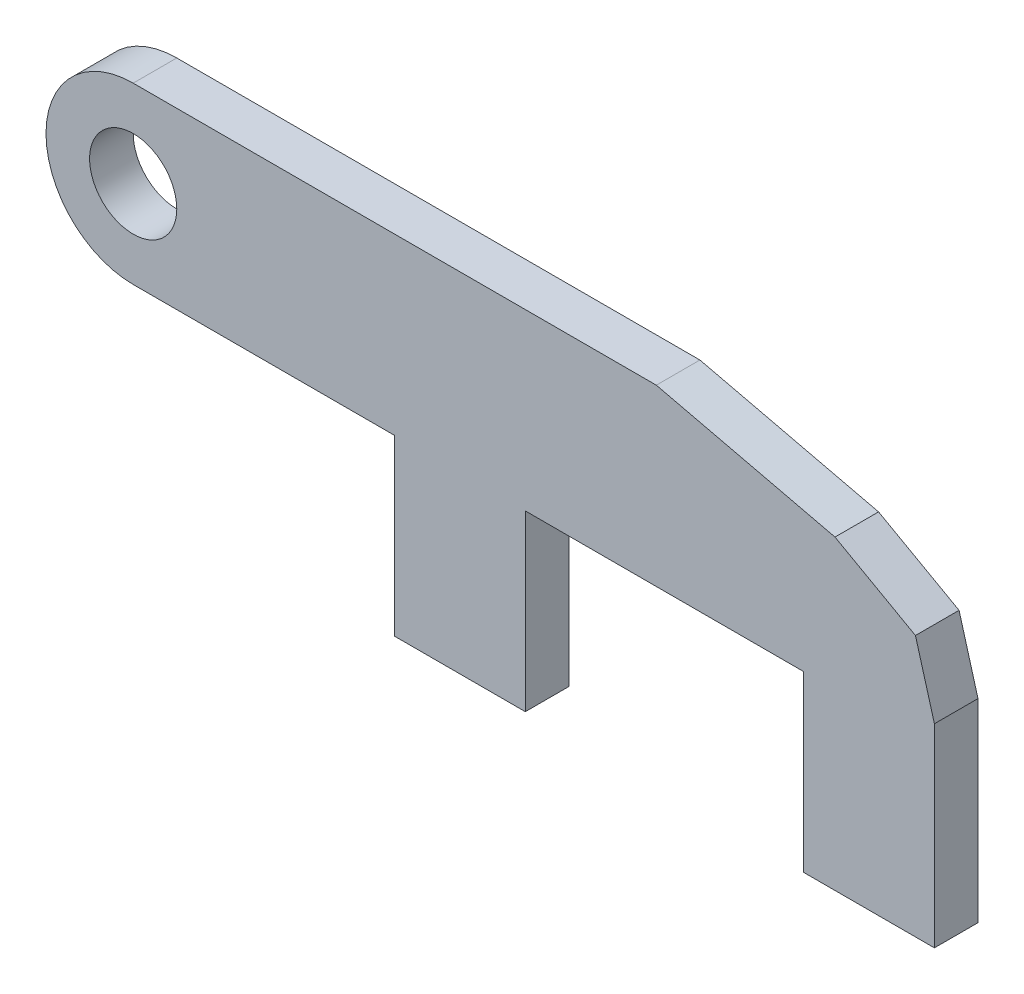
SolidWorks part; units mm, degrees
ref_plane "Front Plane" through (0, 0, 0) normal (0, 0, 1) x (1, 0, 0)
ref_plane "Top Plane" through (0, 0, 0) normal (0, 1, 0) x (1, 0, 0)
ref_plane "Right Plane" through (0, 0, 0) normal (1, 0, 0) x (0, 0, -1)
sketch "Sketch1" plane through (0, 0, 0) normal (0, 0, 1) x (1, 0, 0)
  line L1 (0, 20) -> (60, 20)
  line L2 (60, 20) -> (80.4934, 15.1603)
  line L3 (80.4934, 15.1603) -> (89.7239, 10)
  line L4 (89.7239, 10) -> (91.897, 2.317)
  line L5 (91.897, 2.317) -> (91.897, -19.9463)
  line L6 (91.897, -19.9463) -> (76.897, -19.9463)
  line L7 (76.897, -19.9463) -> (76.897, 0)
  line L8 (76.897, 0) -> (44.9763, 0)
  line L9 (44.9763, 0) -> (44.9763, -19.9463)
  line L10 (44.9763, -19.9463) -> (29.9763, -19.9463)
  line L11 (29.9763, -19.9463) -> (29.9763, 0)
  line L12 (29.9763, 0) -> (0, 0)
  arc A0 (0, 20) -> (0, 0) centre (0, 10) ccw
  circle A1 centre (0, 10) radius 5
  dimension "D1" = 10
  dimension "D5" = 10
  dimension "D2" = 60
  dimension "D3" = 15
  dimension "D4" = 15
extrude "Boss-Extrude1" add sketch "Sketch1" along normal blind 5
